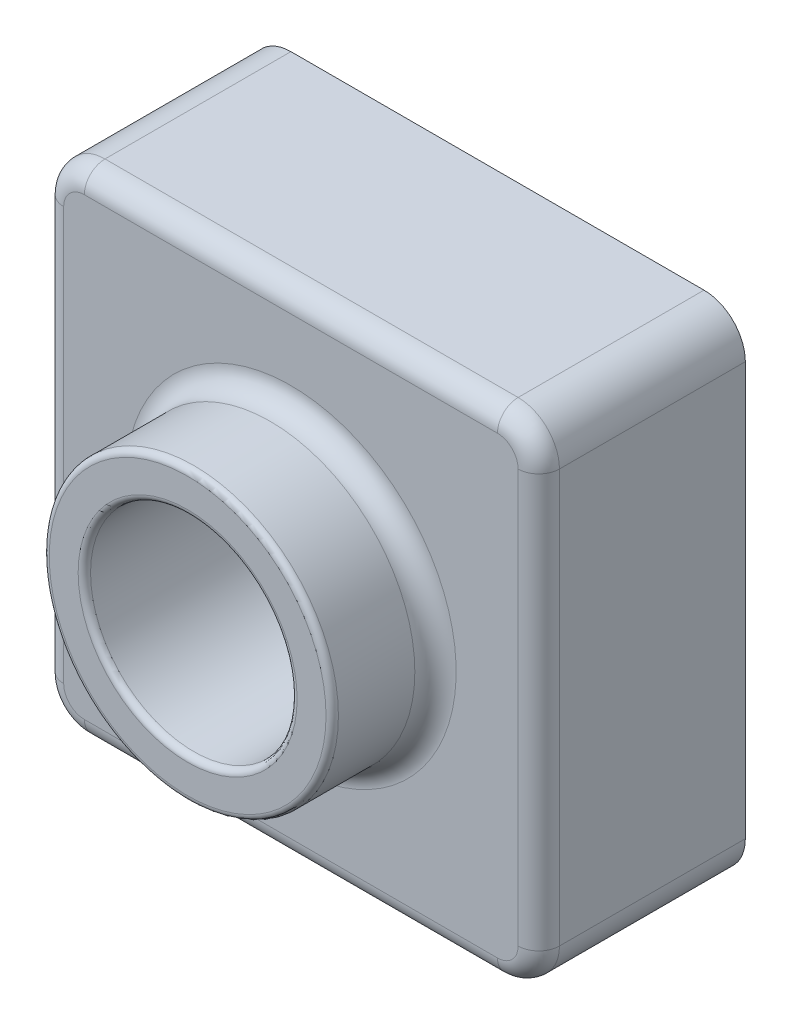
SolidWorks part; units mm, degrees
material "Chrome Stainless Steel"
ref_plane "Front Plane" through (0, 0, 0) normal (0, 0, 1) x (1, 0, 0)
ref_plane "Top Plane" through (0, 0, 0) normal (0, 1, 0) x (1, 0, 0)
ref_plane "Right Plane" through (0, 0, 0) normal (1, 0, 0) x (0, 0, -1)
sketch "Sketch1" plane through (0, 0, 0) normal (0, 0, 1) x (1, 0, 0)
  line L1 (0, 0) -> (120, 0)
  line L2 (0, 0) -> (0, 120)
  line L3 (0, 120) -> (120, 120)
  line L4 (120, 0) -> (120, 120)
  point P5 (3048, 2250.8308)
  dimension "D1" = 120
  dimension "D2" = 120
extrude "Boss-Extrude1" add sketch "Sketch1" along normal blind 50
sketch "Sketch2" plane through (0, 0, 50) normal (0, 0, 1) x (1, 0, 0)
  line L0 (120, 120) -> (0, 120) construction
  line L1 (120, 0) -> (120, 120) construction
  circle A0 centre (60, 60) radius 35
  dimension "D1" = 70
  dimension "D2" = 60
  dimension "D3" = 60
extrude "Boss-Extrude2" add sketch "Sketch2" along normal blind 25
sketch "Sketch3" plane through (0, 0, 75) normal (0, 0, 1) x (1, 0, 0)
  circle A0 centre (60, 60) radius 25
  dimension "D1" = 50
extrude "Cut-Extrude1" cut sketch "Sketch3" against normal through all
fillet "Fillet1" radius 10 4 edges at (0, 0, 25) (120, 0, 25) (0, 120, 25) (120, 120, 25)
fillet "Fillet2" radius 1.5 2 edges at (95, 60, 75) (85, 60, 75)
fillet "Fillet3" radius 5 9 edges at (2.9289, 117.0711, 50) (60, 120, 50) (117.0711, 117.0711, 50) (120, 60, 50) (117.0711, 2.9289, 50) (60, 0, 50) (2.9289, 2.9289, 50) (0, 60, 50) (95, 60, 50)
shell "Shell1" thickness 2
